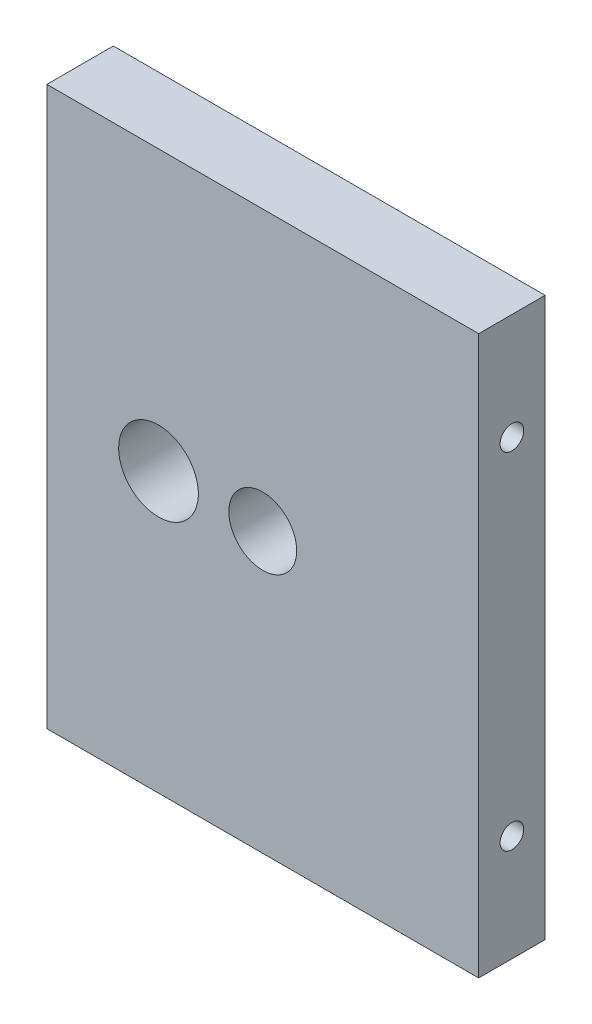
SolidWorks part; units mm, degrees
ref_plane "Front Plane" through (0, 0, 0) normal (0, 0, 1) x (1, 0, 0)
ref_plane "Top Plane" through (0, 0, 0) normal (0, 1, 0) x (1, 0, 0)
ref_plane "Right Plane" through (0, 0, 0) normal (1, 0, 0) x (0, 0, -1)
sketch "Sketch1" plane through (0, 0, 0) normal (0, 0, 1) x (1, 0, 0)
  line L1 (0, 0) -> (32.5, 0)
  line L2 (0, 0) -> (0, 42)
  line L3 (0, 42) -> (32.5, 42)
  line L4 (32.5, 0) -> (32.5, 42)
extrude "Boss-Extrude2" add sketch "Sketch1" along normal blind 5
sketch "Sketch2" plane through (0, 0, 5) normal (0, 0, 1) x (1, 0, 0)
  line L0 (0, 42) -> (0, 34)
  line L1 (0, 42) -> (0, 0) construction
  line L2 (0, 34) -> (32.5, 34)
  line L3 (32.5, 0) -> (32.5, 42) construction
  line L4 (0, 0) -> (0, 8)
  line L5 (0, 8) -> (32.5, 8)
sketch "Sketch3" plane through (0, 0, 0) normal (-1, 0, 0) x (0, 0, 1)
  line L0 (5, 34) -> (0, 34)
  line L1 (5, 42) -> (5, 34) construction
  line L2 (0, 42) -> (0, 0) construction
  line L3 (5, 8) -> (0, 8)
  line L4 (5, 0) -> (5, 8) construction
  line L5 (5, 42) -> (5, 0) construction
  point P12 (5, 34)
  point P14 (5, 8)
hole_wizard "#2-56 Tapped Hole1" positions "Sketch4" profile "Sketch5" tap size "#2-56" standard "ANSI Inch"
sketch "Sketch4" plane through (0, 0, 0) normal (-1, 0, 0) x (0, 0, 1)
  line L0 (5, 34) -> (0, 34) construction
  line L1 (5, 8) -> (0, 8) construction
  point P0 (2.5, 34)
  point P4 (2.5, 8)
sketch "Sketch5" plane through (0, 34, 2.5) normal (0, 1, 0) x (0, 0, 1)
  line L0 (0, 0) -> (0, 8)
  line L1 (0, 8) -> (0.889, 7.4658)
  line L2 (0.889, 7.4658) -> (0.889, 0)
  line L5 (0.889, 0) -> (0, 0)
  line L10 (0, 8) -> (-0.889, 7.4658) construction
  line L11 (0, -6.35) -> (0, 107.95) construction
  dimension "Tap Drill Dia." = 1.778
  dimension "Tap Drill Depth" = 8
  dimension "Drill Angle" = 118
cosmetic thread "Hole Thread1" parameters "D1"=4.37, "D2"=2.1844
cosmetic thread "Hole Thread2" parameters "D1"=4.37, "D2"=2.1844
sketch "Sketch6" plane through (32.5, 0, 0) normal (1, 0, 0) x (0, 0, -1)
  line L0 (-5, 34) -> (0, 34)
  line L1 (-5, 8) -> (0, 8)
hole_wizard "#2-56 Tapped Hole2" positions "Sketch7" profile "Sketch8" tap size "#2-56" standard "ANSI Inch"
sketch "Sketch7" plane through (32.5, 0, 0) normal (1, 0, 0) x (0, 0, -1)
  point P0 (-2.5, 34)
  point P3 (-2.5, 8)
sketch "Sketch8" plane through (32.5, 34, 2.5) normal (0, 1, 0) x (0, 0, -1)
  line L0 (0, 0) -> (0, 8)
  line L1 (0, 8) -> (0.889, 7.4658)
  line L2 (0.889, 7.4658) -> (0.889, 0)
  line L5 (0.889, 0) -> (0, 0)
  line L10 (0, 8) -> (-0.889, 7.4658) construction
  line L11 (0, -6.35) -> (0, 107.95) construction
  dimension "Tap Drill Dia." = 1.778
  dimension "Tap Drill Depth" = 8
  dimension "Drill Angle" = 118
cosmetic thread "Hole Thread3" parameters "D1"=4.37, "D2"=2.1844
cosmetic thread "Hole Thread4" parameters "D1"=4.37, "D2"=2.1844
sketch "Sketch9" plane through (0, 0, 0) normal (0, 0, -1) x (-1, 0, 0)
  line L0 (0, 21) -> (-32.5, 21)
  line L1 (0, 42) -> (0, 0) construction
  line L2 (-32.5, 0) -> (-32.5, 42) construction
  line L3 (-16.25, 21) -> (-8.4, 21)
  circle A0 centre (-8.4, 21) radius 3
extrude "Cut-Extrude1" cut sketch "Sketch9" against normal blind 5 contours L0 A0 | L0 A0
sketch "Sketch10" plane through (0, 0, 0) normal (0, 0, -1) x (-1, 0, 0)
  line L0 (-32.5, 42) -> (0, 0)
hole_wizard "1/4-20 Tapped Hole1" positions "Sketch11" profile "Sketch12" tap size "1/4-20" standard "ANSI Inch" end condition through all
sketch "Sketch11" plane through (0, 0, 0) normal (0, 0, -1) x (-1, 0, 0)
  line L0 (-32.5, 42) -> (0, 0) construction
  point P0 (-16.25, 21)
sketch "Sketch12" plane through (16.25, 21, 0) normal (1, 0, 0) x (0, 1, 0)
  line L0 (0, 0) -> (0, 5)
  line L1 (0, 5) -> (2.5527, 5)
  line L2 (2.5527, 5) -> (2.5527, 0)
  line L5 (2.5527, 0) -> (0, 0)
  line L11 (0, -6.35) -> (0, 107.95) construction
  dimension "Thru Tap Drill Dia." = 5.1054
  dimension "Thru Tap Drill Depth" = 5
cosmetic thread "Hole Thread5" parameters "D2"=6.35
